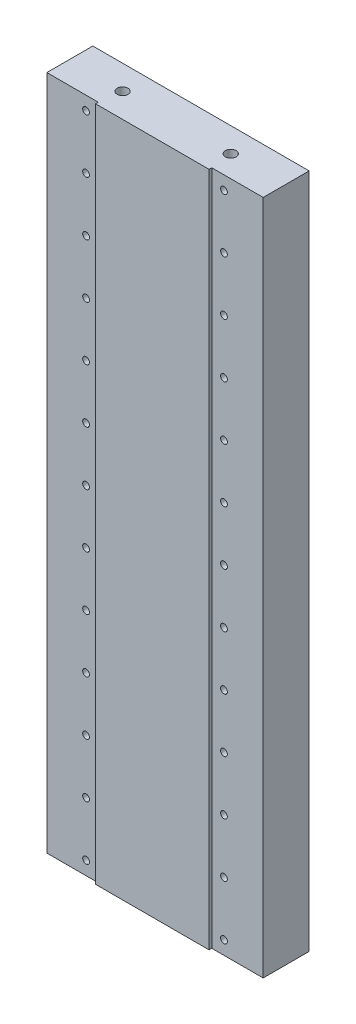
SolidWorks part; units mm, degrees
ref_plane "Alzado" through (0, 0, 0) normal (0, 0, 1) x (1, 0, 0)
ref_plane "Planta" through (0, 0, 0) normal (0, 1, 0) x (1, 0, 0)
ref_plane "Vista lateral" through (0, 0, 0) normal (1, 0, 0) x (0, 0, -1)
sketch "Croquis1" plane through (0, 0, 0) normal (0, 0, 1) x (1, 0, 0)
  line L1 (0, 0) -> (80, 0)
  line L2 (0, 0) -> (0, 250)
  line L3 (0, 250) -> (80, 250)
  line L4 (80, 0) -> (80, 250)
  dimension "D1" = 250
  dimension "D2" = 80
extrude "Saliente-Extruir1" add sketch "Croquis1" along normal blind 18
sketch "Croquis2" plane through (0, 0, 18) normal (0, 0, 1) x (1, 0, 0)
  line L0 (80, 250) -> (0, 250) construction
  line L1 (0, 0) -> (19, 0)
  line L2 (0, 0) -> (0, 250)
  line L3 (0, 250) -> (19, 250)
  line L4 (19, 0) -> (19, 250)
  line L6 (80, 0) -> (61, 0)
  line L7 (80, 0) -> (80, 250)
  line L8 (80, 250) -> (61, 250)
  line L9 (61, 0) -> (61, 250)
  line L11 (80, 0) -> (80, 250) construction
  line L12 (0, 250) -> (0, 0) construction
  line L13 (0, 0) -> (80, 0) construction
  dimension "D1" = 19
  dimension "D2" = 19
extrude "Cortar-Extruir1" cut sketch "Croquis2" against normal blind 1
hole_wizard "Taladro roscado M31" positions "Croquis3" profile "Croquis4" tap size "M3" standard "DIN"
sketch "Croquis3" plane through (0, 0, 17) normal (0, 0, 1) x (1, 0, 0)
  line L0 (19, 250) -> (0, 250) construction
  line L2 (19, 0) -> (19, 250) construction
  point P0 (14.5, 245)
  dimension "D1" = 5
  dimension "D2" = 4.5
sketch "Croquis4" plane through (14.5, 245, 17) normal (1, 0, 0) x (0, -1, 0)
  line L0 (0, 0) -> (0, 10.7511)
  line L1 (0, 10.7511) -> (1.25, 10)
  line L2 (1.25, 10) -> (1.25, 0)
  line L5 (1.25, 0) -> (0, 0)
  line L10 (0, 10.7511) -> (-1.25, 10) construction
  line L11 (0, -6.35) -> (0, 107.95) construction
  dimension "Diámetro de perforador para roscar" = 2.5
  dimension "Profundidad de perforador para roscar" = 10
  dimension "Ángulo de perforador" = 118
cosmetic thread "Rosca de taladro2" parameters "D1"=6, "D2"=3
pattern_linear "MatrizL1" count 13 spacing 20 along (0, -1, 0) count 2 spacing 51 along (1, 0, 0) of "Taladro roscado M31"
hole_wizard "Taladros de espiga de Ø4.0mm1" positions "Croquis5" profile "Croquis7" hole size "Ø4.0" standard "DIN"
sketch "Croquis5" plane through (0, 250, 0) normal (0, 1, 0) x (1, 0, 0)
  line L0 (80, 0) -> (0, 0) construction
  line L1 (0, -17) -> (0, 0) construction
  line L2 (80, -17) -> (80, 0) construction
  point P0 (60, -9)
  point P2 (20, -9)
  dimension "D1" = 9
  dimension "D2" = 9
  dimension "D3" = 20
  dimension "D4" = 20
sketch "Croquis7" plane through (60, 250, 9) normal (1, 0, 0) x (0, 0, 1)
  line L0 (0, 0) -> (0, 13.2017)
  line L1 (0, 13.2017) -> (2, 12)
  line L2 (2, 12) -> (2, 0)
  line L5 (2, 0) -> (0, 0)
  line L10 (0, 13.2017) -> (-2, 12) construction
  line L11 (0, -6.35) -> (0, 107.95) construction
  dimension "Diámetro de taladro" = 4
  dimension "Profundidad de taladro" = 12
  dimension "Ángulo de perforador" = 118
hole_wizard "Taladro roscado M32" [suppressed] positions "Croquis8" profile "Croquis9" tap size "M3" standard "DIN"
sketch "Croquis8" plane through (0, 0, 16) normal (0, 0, 1) x (1, 0, 0)
  line L0 (19, 0) -> (19, 250) construction
  line L1 (19, 250) -> (0, 250) construction
  point P0 (13, 239)
  dimension "D1" = 6
  dimension "D2" = 11
sketch "Croquis9" plane through (13, 239, 16) normal (1, 0, 0) x (0, -1, 0)
  line L0 (0, 0) -> (0, 10.7511)
  line L1 (0, 10.7511) -> (1.25, 10)
  line L2 (1.25, 10) -> (1.25, 0)
  line L5 (1.25, 0) -> (0, 0)
  line L10 (0, 10.7511) -> (-1.25, 10) construction
  line L11 (0, -6.35) -> (0, 107.95) construction
  dimension "Diámetro de perforador para roscar" = 2.5
  dimension "Profundidad de perforador para roscar" = 10
  dimension "Ángulo de perforador" = 118
cosmetic thread "Rosca de taladro3" [suppressed] parameters "D1"=6, "D2"=3
pattern_linear "MatrizL2" [suppressed] count 10 spacing 25 count 2 spacing 54
hole_wizard "Taladro roscado M41" positions "Croquis10" profile "Croquis12" tap size "M4" standard "DIN"
sketch "Croquis10" plane through (0, 0, 0) normal (0, 0, -1) x (-1, 0, 0)
  line L1 (-73.5, 196) -> (-6.5, 196) construction
  line L2 (-73.5, 196) -> (-73.5, 237) construction
  line L3 (-73.5, 237) -> (-6.5, 237) construction
  line L4 (-6.5, 196) -> (-6.5, 237) construction
  line L5 (-80, 250) -> (0, 250) construction
  line L6 (-80, 0) -> (-80, 250) construction
  line L7 (0, 250) -> (0, 0) construction
  point P1 (-73.5, 196)
  point P2 (-6.5, 237)
  point P107 (-73.5, 237)
  point P108 (-6.5, 196)
  dimension "D1" = 13
  dimension "D2" = 41
  dimension "D3" = 6.5
  dimension "D4" = 6.5
sketch "Croquis12" plane through (73.5, 196, 0) normal (1, 0, 0) x (0, 1, 0)
  line L0 (0, 0) -> (0, 12.4914)
  line L1 (0, 12.4914) -> (1.65, 11.5)
  line L2 (1.65, 11.5) -> (1.65, 0)
  line L5 (1.65, 0) -> (0, 0)
  line L10 (0, 12.4914) -> (-1.65, 11.5) construction
  line L11 (0, -6.35) -> (0, 107.95) construction
  dimension "Diámetro de perforador para roscar" = 3.3
  dimension "Profundidad de perforador para roscar" = 11.5
  dimension "Ángulo de perforador" = 118
cosmetic thread "Rosca de taladro4" parameters "D1"=8, "D2"=4
cosmetic thread "Rosca de taladro5" parameters "D1"=8, "D2"=4
cosmetic thread "Rosca de taladro6" parameters "D1"=8, "D2"=4
cosmetic thread "Rosca de taladro7" parameters "D1"=8, "D2"=4
